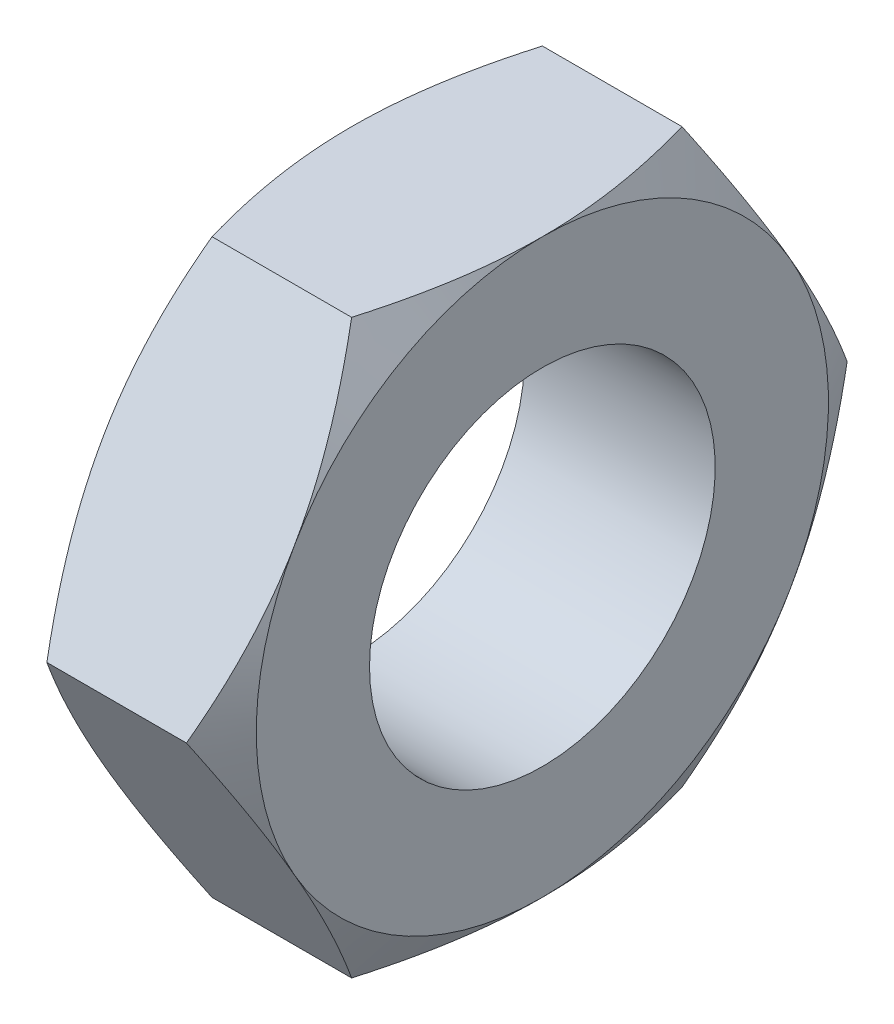
SolidWorks part; units mm, degrees
material "Alloy Steel"
ref_plane "Front Plane" through (0, 0, 0) normal (0, 0, 1) x (1, 0, 0)
ref_plane "Top Plane" through (0, 0, 0) normal (0, 1, 0) x (1, 0, 0)
ref_plane "Right Plane" through (0, 0, 0) normal (1, 0, 0) x (0, 0, -1)
sketch "Sketch1" plane through (0, 0, 0) normal (1, 0, 0) x (0, 0, -1)
  line L1 (13.8564, 0) -> (6.9282, 12)
  line L2 (6.9282, 12) -> (-6.9282, 12)
  line L3 (-6.9282, 12) -> (-13.8564, 0)
  line L4 (-13.8564, 0) -> (-6.9282, -12)
  line L5 (-6.9282, -12) -> (6.9282, -12)
  line L6 (6.9282, -12) -> (13.8564, 0)
  circle A0 centre (0, 0) radius 12 construction
  dimension "D1" = 24
extrude "Boss-Extrude1" add sketch "Sketch1" along normal blind 8
hole_wizard " Tapped Hole1" positions "Sketch5" profile "Sketch4" tap size "M16x1.5" standard "Ansi Metric" end condition through all
sketch "Sketch5" plane through (0, 0, 0) normal (-1, 0, 0) x (0, 0, 1)
  point P0 (0, 0)
sketch "Sketch4" plane through (0, 0, 0) normal (0, 1, 0) x (0, 0, 1)
  line L0 (0, 0) -> (0, 8)
  line L1 (0, 8) -> (7.25, 8)
  line L2 (7.25, 8) -> (7.25, 0)
  line L5 (7.25, 0) -> (0, 0)
  line L11 (0, -6.35) -> (0, 107.95) construction
  dimension "Thru Tap Drill Dia." = 14.5
  dimension "Thru Tap Drill Depth" = 8
cosmetic thread "Hole Thread1" parameters "D2"=16
sketch "Sketch6" plane through (0, 0, 0) normal (0, 1, 0) x (1, 0, 0)
  line L0 (0, 0) -> (10.1923, 0) construction
  line L1 (0, 12) -> (1.0718, 13.8564)
  line L5 (1.0718, 13.8564) -> (0, 13.8564)
  line L6 (0, 13.8564) -> (0, 12)
  dimension "D1" = 12
  dimension "D2" = 30
revolve "Cut-Revolve1" cut sketch "Sketch6" angle 360 about L0
ref_plane "Plane1" through (4, 0, 0) normal (-1, 0, 0) x (0, 0, 1)
mirror "Mirror1" about plane through (4, 0, 0) normal (-1, 0, 0) of "Cut-Revolve1"
